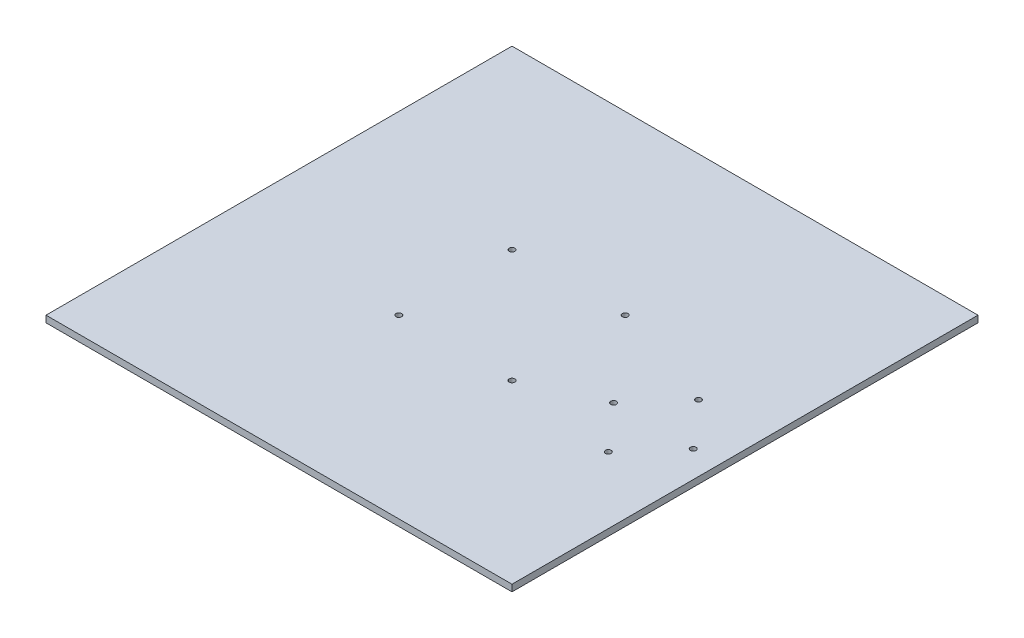
SolidWorks part; units mm, degrees
ref_plane "Front Plane" through (0, 0, 0) normal (0, 0, 1) x (1, 0, 0)
ref_plane "Top Plane" through (0, 0, 0) normal (0, 1, 0) x (1, 0, 0)
ref_plane "Right Plane" through (0, 0, 0) normal (1, 0, 0) x (0, 0, -1)
sketch "Sketch1" plane through (0, 0, 0) normal (0, 1, 0) x (1, 0, 0)
  line L1 (-111.125, -111.125) -> (111.125, -111.125)
  line L2 (-111.125, -111.125) -> (-111.125, 111.125)
  line L3 (-111.125, 111.125) -> (111.125, 111.125)
  line L4 (111.125, -111.125) -> (111.125, 111.125)
  dimension "D1" = 222.25
  dimension "D2" = 222.25
extrude "Boss-Extrude1" add sketch "Sketch1" along normal blind 3.175
sketch "Sketch2" plane through (0, 3.175, 0) normal (0, 1, 0) x (1, 0, 0)
  line L0 (0, -111.125) -> (0, 111.125) construction
  line L1 (111.125, 111.125) -> (-111.125, 111.125) construction
  line L2 (-111.125, -111.125) -> (111.125, -111.125) construction
  line L3 (-26.9875, 0) -> (26.9875, 0) construction
  line L4 (-26.9875, 26.9875) -> (26.9875, 26.9875) construction
  line L5 (-26.9875, 26.9875) -> (-26.9875, -26.9875) construction
  line L6 (-26.9875, -26.9875) -> (26.9875, -26.9875) construction
  line L7 (26.9875, 26.9875) -> (26.9875, -26.9875) construction
  point P12 (0, 0)
  point P13 (0, 0)
  dimension "D1" = 53.975
  dimension "D2" = 53.975
hole_wizard "#6-32 Tapped Hole1" positions "Sketch4" profile "Sketch3" tap size "#6-32" standard "ANSI Inch" end condition through all
sketch "Sketch4" plane through (0, 3.175, 0) normal (0, 1, 0) x (1, 0, 0)
  point P0 (-26.9875, -26.9875)
  point P3 (-26.9875, 26.9875)
  point P6 (26.9875, 26.9875)
  point P9 (26.9875, -26.9875)
sketch "Sketch3" plane through (-26.9875, 3.175, 26.9875) normal (1, 0, 0) x (0, 0, 1)
  line L0 (0, 0) -> (0, 3.175)
  line L1 (0, 3.175) -> (1.3525, 3.175)
  line L2 (1.3525, 3.175) -> (1.3525, 0)
  line L5 (1.3525, 0) -> (0, 0)
  line L11 (0, -6.35) -> (0, 107.95) construction
  dimension "Thru Tap Drill Dia." = 2.7051
  dimension "Thru Tap Drill Depth" = 3.175
cosmetic thread "Hole Thread1" parameters "D2"=3.5052
cosmetic thread "Hole Thread2" parameters "D2"=3.5052
cosmetic thread "Hole Thread3" parameters "D2"=3.5052
cosmetic thread "Hole Thread4" parameters "D2"=3.5052
sketch "Sketch5" plane through (0, 3.175, 0) normal (0, 1, 0) x (1, 0, 0)
  line L1 (60.425, -33.5) -> (98.425, -33.5) construction
  line L2 (60.425, -33.5) -> (60.425, 9.5) construction
  line L3 (60.425, 9.5) -> (98.425, 9.5) construction
  line L4 (98.425, -33.5) -> (98.425, 9.5) construction
  line L7 (-111.125, 0) -> (111.125, 0) construction
  line L8 (-111.125, 111.125) -> (-111.125, -111.125) construction
  line L9 (111.125, -111.125) -> (111.125, 111.125) construction
  point P4 (79.425, 9.5)
  point P5 (79.425, -33.5)
  point P7 (98.425, -12)
  point P8 (60.425, -12)
  dimension "D1" = 43
  dimension "D2" = 38
  dimension "D3" = 12.7
  dimension "D4" = 9.5
hole_wizard "#6-32 Tapped Hole3" positions "Sketch9" profile "Sketch8" tap size "#6-32" standard "ANSI Inch" end condition through all
sketch "Sketch9" plane through (0, 3.175, 0) normal (0, 1, 0) x (1, 0, 0)
  point P0 (60.425, -12)
  point P3 (79.425, -33.5)
  point P6 (98.425, -12)
  point P9 (79.425, 9.5)
sketch "Sketch8" plane through (60.425, 3.175, 12) normal (1, 0, 0) x (0, 0, 1)
  line L0 (0, 0) -> (0, 3.175)
  line L1 (0, 3.175) -> (1.3525, 3.175)
  line L2 (1.3525, 3.175) -> (1.3525, 0)
  line L5 (1.3525, 0) -> (0, 0)
  line L11 (0, -6.35) -> (0, 107.95) construction
  dimension "Thru Tap Drill Dia." = 2.7051
  dimension "Thru Tap Drill Depth" = 3.175
cosmetic thread "Hole Thread9" parameters "D2"=3.5052
cosmetic thread "Hole Thread10" parameters "D2"=3.5052
cosmetic thread "Hole Thread11" parameters "D2"=3.5052
cosmetic thread "Hole Thread12" parameters "D2"=3.5052
